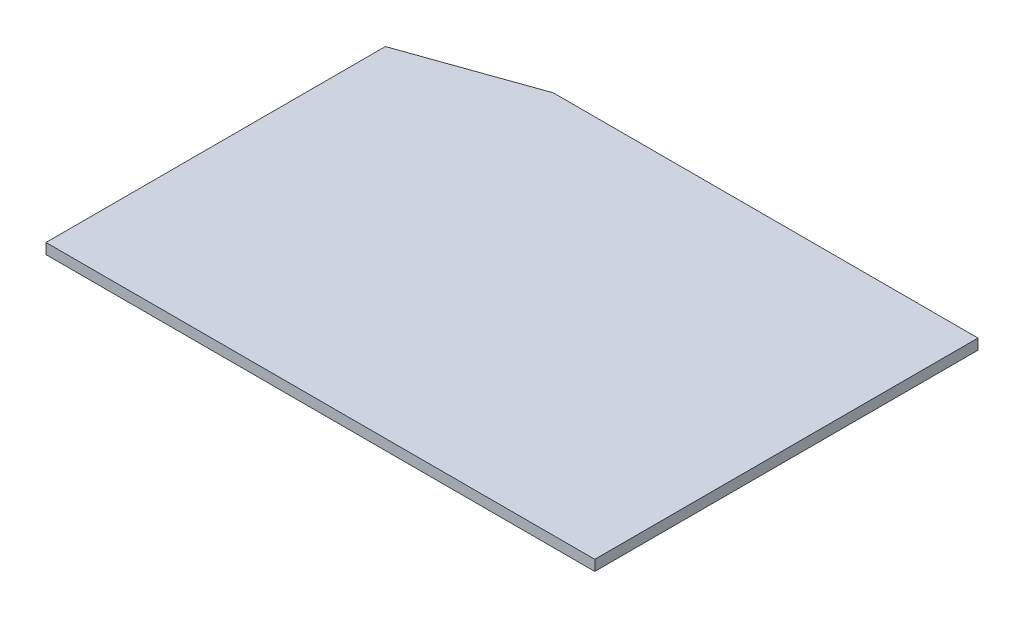
SolidWorks part; units mm, degrees
ref_plane "Plan de face" through (0, 0, 0) normal (0, 0, 1) x (1, 0, 0)
ref_plane "Plan de dessus" through (0, 0, 0) normal (0, 1, 0) x (1, 0, 0)
ref_plane "Plan de droite" through (0, 0, 0) normal (1, 0, 0) x (0, 0, -1)
sketch "Esquisse1" plane through (0, 0, 0) normal (0, 1, 0) x (1, 0, 0)
  line L0 (0, 0) -> (104.1497, 0)
  line L1 (104.1497, 0) -> (104.1497, 72.7353)
  line L2 (104.1497, 72.7353) -> (23.5343, 72.7353)
  line L3 (23.5343, 72.7353) -> (0, 64.4065)
  line L4 (0, 64.4065) -> (0, 0)
  point P5 (0, 0)
extrude "Boss.-Extru.1" add sketch "Esquisse1" along normal blind 2
